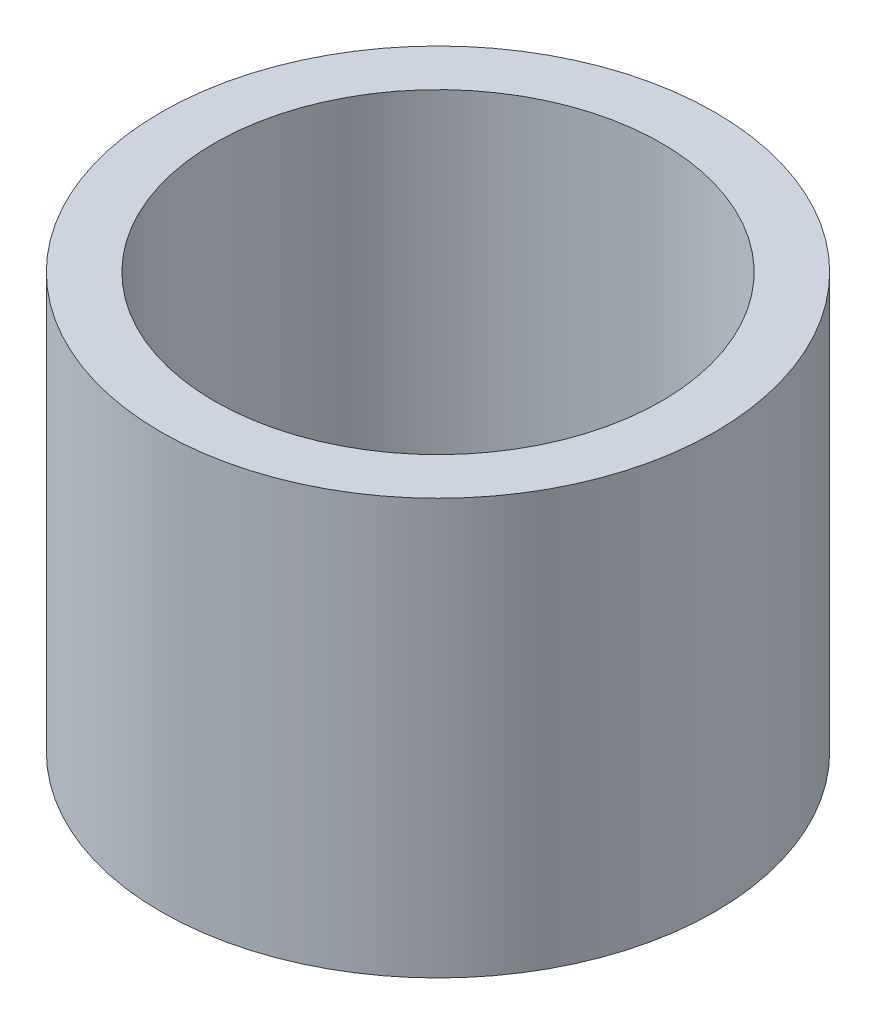
SolidWorks part; units mm, degrees
ref_plane "前视基准面" through (0, 0, 0) normal (0, 0, 1) x (1, 0, 0)
ref_plane "上视基准面" through (0, 0, 0) normal (0, 1, 0) x (1, 0, 0)
ref_plane "右视基准面" through (0, 0, 0) normal (1, 0, 0) x (0, 0, -1)
sketch "草图1" plane through (0, 0, 0) normal (0, 0, 1) x (1, 0, 0)
  line L0 (0, 161.3762) -> (0, 0) construction
  line L1 (141.7365, 0) -> (-131.7984, 0) construction
  line L2 (25.4, 0) -> (25.4, 38.1)
  line L3 (20.5, 38.1) -> (25.4, 38.1)
  line L4 (20.5, 0) -> (25.4, 0)
  line L7 (20.5, 38.1) -> (20.5, 0)
  dimension "D2" = 25.4
  dimension "D3" = 38.1
  dimension "D11" = 20.5
revolve "旋转1" add sketch "草图1" angle 360 about L0
cosmetic thread "装饰螺纹线1" parameters "D2"=42
